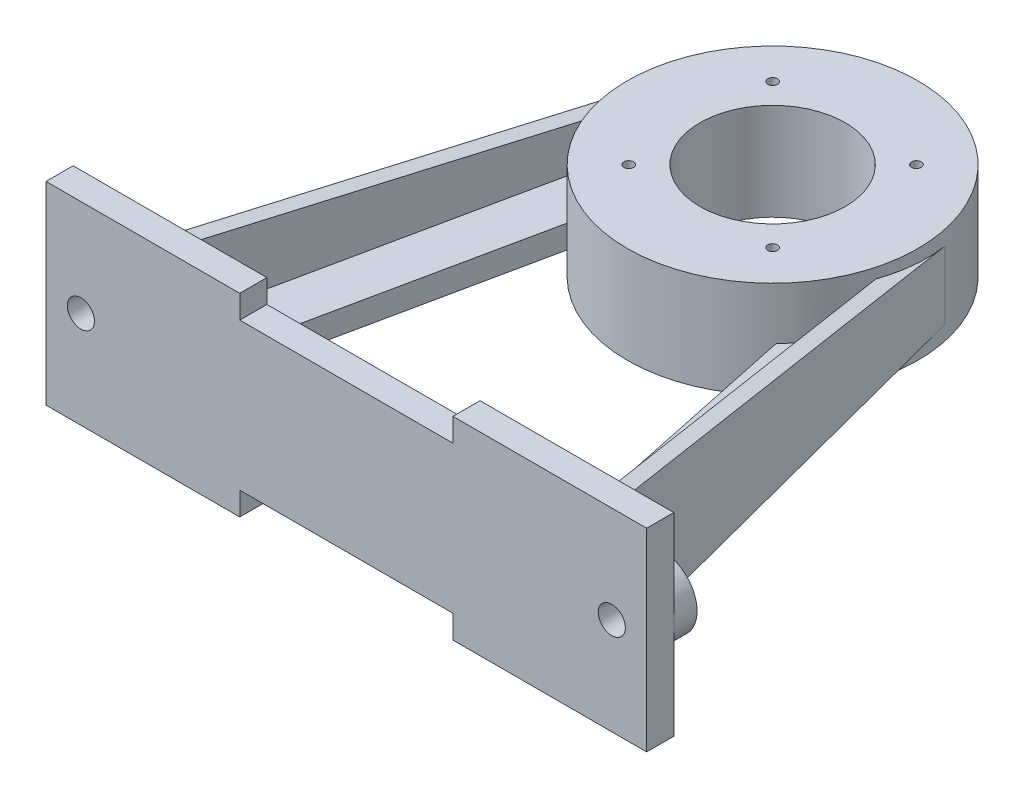
SolidWorks part; units mm, degrees
ref_plane "Front Plane" through (0, 0, 0) normal (0, 0, 1) x (1, 0, 0)
ref_plane "Top Plane" through (0, 0, 0) normal (0, 1, 0) x (1, 0, 0)
ref_plane "Right Plane" through (0, 0, 0) normal (1, 0, 0) x (0, 0, -1)
sketch "Sketch1" plane through (0, 0, 0) normal (0, 0, 1) x (1, 0, 0)
  line L0 (-176.7021, 0) -> (195.4255, 0) construction
  line L1 (-155, 50) -> (-55, 50)
  line L2 (-155, 50) -> (-155, -50)
  line L3 (-155, -50) -> (-55, -50)
  line L4 (155, 50) -> (155, -50)
  line L5 (-155, 50) -> (155, -50) construction
  line L6 (-155, -50) -> (155, 50) construction
  line L7 (-55, 50) -> (-55, 38)
  line L8 (-55, 38) -> (55, 38)
  line L9 (55, 38) -> (55, 50)
  line L10 (55, -38) -> (55, -50)
  line L11 (-55, -38) -> (55, -38)
  line L12 (-55, -50) -> (-55, -38)
  line L13 (55, 50) -> (155, 50)
  line L14 (55, -50) -> (155, -50)
  point P0 (0, 0)
  dimension "D1" = 110
  dimension "D2" = 100
  dimension "D3" = 12
extrude "Boss-Extrude1" add sketch "Sketch1" along normal blind 14
sketch "Sketch2" plane through (0, 0, 0) normal (0, 1, 0) x (1, 0, 0)
  line L0 (55, -14) -> (-55, -14) construction
  circle A0 centre (0, 206) radius 75
  circle A1 centre (0, 206) radius 37.5
  dimension "D1" = 150
  dimension "D2" = 220
  dimension "D3" = 75
extrude "Boss-Extrude2" add sketch "Sketch2" along normal mid plane 50 separate body
hole_wizard "M6 Tapped Hole1" positions "Sketch4" profile "Sketch5" tap size "M6" standard "AS" end condition through all
sketch "Sketch4" plane through (0, 25, 0) normal (0, 1, 0) x (1, 0, 0)
  line L0 (-75, 206) -> (75, 206) construction
  line L2 (0, 281) -> (0, 131) construction
  line L4 (-37.1231, 243.1231) -> (0, 206) construction
  circle A0 centre (0, 206) radius 75 construction
  circle A1 centre (0, 206) radius 52.5 construction
  point P0 (-37.1231, 243.1231)
  dimension "D1" = 105
  dimension "D2" = 45
sketch "Sketch5" plane through (-37.1231, 25, -243.1231) normal (1, 0, 0) x (0, 0, 1)
  line L0 (0, 0) -> (0, 50)
  line L1 (0, 50) -> (2.5, 50)
  line L2 (2.5, 50) -> (2.5, 0)
  line L5 (2.5, 0) -> (0, 0)
  line L11 (0, -6.35) -> (0, 107.95) construction
  dimension "Thru Tap Drill Dia." = 5
  dimension "Thru Tap Drill Depth" = 50
cosmetic thread "Hole Thread1" parameters "D2"=6
pattern_circular "CirPattern1" count 4 over 360 about axis through (0, 0, -206) along (0, 1, 0) of "M6 Tapped Hole1"
sketch "Sketch7" plane through (0, 0, 0) normal (0, 1, 0) x (1, 0, 0)
  line L0 (-55, 0) -> (-155, 0) construction
  line L1 (-111.8247, 0) -> (-120, 0)
  line L2 (-73.3921, 221.4468) -> (-120, 0)
  line L3 (-111.8247, 0) -> (-72.5053, 186.8172)
  circle A0 centre (0, 206) radius 75 construction
  arc A1 (-73.3921, 221.4468) -> (-72.5053, 186.8172) centre (0, 206) ccw
  dimension "D1" = 8
  dimension "D2" = 35
extrude "Boss-Extrude3" add sketch "Sketch7" along normal mid plane 35
sketch "Sketch8" plane through (-114.9098, 0, -24.1851) normal (-0.9786, 0, -0.206) x (-0.206, 0, 0.9786)
  line L0 (-304.3665, 0) -> (68.5414, 0) construction
  line L1 (-201.5835, 17.5) -> (24.7149, 32.5)
  line L2 (-201.5835, 17.5) -> (24.7149, 17.5) construction
  line L3 (-201.5835, 17.5) -> (24.7149, 17.5)
  line L4 (24.7149, 32.5) -> (24.7149, 17.5)
  line L5 (24.7149, -32.5) -> (24.7149, -17.5)
  line L6 (-201.5835, -17.5) -> (24.7149, -17.5)
  line L7 (-201.5835, -17.5) -> (24.7149, -32.5)
  dimension "D1" = 65
extrude "Boss-Extrude4" add sketch "Sketch8" against normal blind 8
sketch "Sketch9" plane through (0, 0, 0) normal (0, 0, -1) x (-1, 0, 0)
  line L0 (111.8247, 32.3884) -> (111.8247, -32.3884) construction
  line L1 (111.8247, 18) -> (111.8247, -18)
  line L2 (111.8247, 18) -> (137, 18)
  line L3 (-225.7536, 0) -> (183.9113, 0) construction
  line L4 (111.8247, -18) -> (137, -18)
  line L5 (155, 50) -> (155, -50) construction
  arc A0 (137, -18) -> (137, 18) centre (137, 0) ccw
  circle A1 centre (137, 0) radius 7
  dimension "D1" = 18
  dimension "D2" = 14
extrude "Boss-Extrude5" add sketch "Sketch9" along normal blind 12
sketch "Sketch10" plane through (0, 0, 0) normal (0, 0, -1) x (-1, 0, 0)
  circle A1 centre (137, 0) radius 7
  circle A2 centre (137, 0) radius 7
  dimension "D1" = 0
extrude "Cut-Extrude1" cut sketch "Sketch10" against normal up to next (14 mm away)
mirror "Mirror3" about plane through (0, 0, 0) normal (1, 0, 0) of "Boss-Extrude3", "Boss-Extrude5", "Cut-Extrude1", "Boss-Extrude4"
ref_plane "Plane1" through (0, -2, 0) normal (0, 1, 0) x (1, 0, 0)
sketch "Sketch13" plane through (0, -2, 0) normal (0, 1, 0) x (1, 0, 0)
  line L0 (-111.8247, 0) -> (-72.5053, 186.8172) construction
  line L1 (111.8247, 0) -> (72.5053, 186.8172) construction
  line L2 (155, 0) -> (55, 0) construction
  line L4 (-111.8247, 0) -> (-72.5053, 186.8172)
  line L5 (111.8247, 0) -> (72.5053, 186.8172)
  line L6 (111.8247, 0) -> (55, 0)
  line L7 (55, 0) -> (-111.8247, 0)
  line L8 (-53.8971, 153.8454) -> (-82.4885, 18)
  line L9 (-82.4885, 18) -> (82.4885, 18)
  line L10 (0, 206) -> (0, 0) construction
  line L11 (53.8971, 153.8454) -> (82.4885, 18)
  circle A0 centre (0, 206) radius 75 construction
  arc A1 (-72.5053, 186.8172) -> (-53.8971, 153.8454) centre (0, 206) ccw
  arc A2 (53.8971, 153.8454) -> (72.5053, 186.8172) centre (0, 206) ccw
  point P15 (0, 18)
  dimension "D1" = 18
  dimension "D2" = 25
extrude "Boss-Extrude6" add sketch "Sketch13" against normal blind 12
fillet "Fillet1" radius 10 2 edges at (82.4885, -8, -18) (-82.4885, -8, -18)
